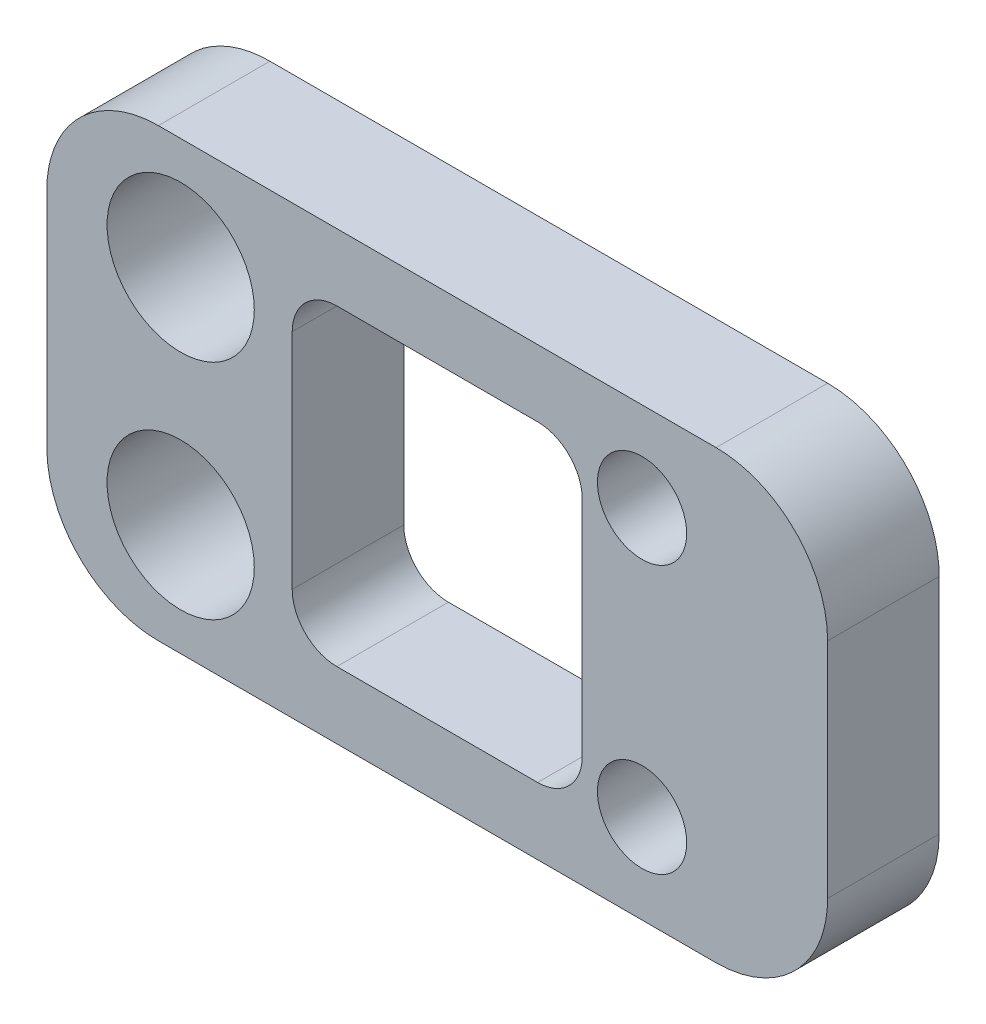
SolidWorks part; units mm, degrees
ref_plane "Plan de face" through (0, 0, 0) normal (0, 0, 1) x (1, 0, 0)
ref_plane "Plan de dessus" through (0, 0, 0) normal (0, 1, 0) x (1, 0, 0)
ref_plane "Plan de droite" through (0, 0, 0) normal (1, 0, 0) x (0, 0, -1)
sketch "Esquisse1" plane through (0, 0, 0) normal (0, 0, 1) x (1, 0, 0)
  line L1 (-48.7729, 33.8508) -> (-13.7729, 33.8508)
  line L2 (-48.7729, 33.8508) -> (-48.7729, 13.8508)
  line L3 (-48.7729, 13.8508) -> (-13.7729, 13.8508)
  line L4 (-13.7729, 33.8508) -> (-13.7729, 13.8508)
  line L5 (-48.7729, 33.8508) -> (-13.7729, 13.8508) construction
  line L6 (-48.7729, 13.8508) -> (-13.7729, 33.8508) construction
  point P0 (-31.2729, 23.8508)
  dimension "D1" = 20
  dimension "D2" = 35
extrude "Boss.-Extru.1" add sketch "Esquisse1" along normal blind 5
fillet "Congé1" radius 5 4 edges at (-13.7729, 13.8508, 2.5) (-13.7729, 33.8508, 2.5) (-48.7729, 13.8508, 2.5) (-48.7729, 33.8508, 2.5)
sketch "Esquisse6" plane through (0, 0, 5) normal (0, 0, 1) x (1, 0, 0)
  line L1 (-43.7729, 33.8508) -> (-18.7729, 33.8508) construction
  line L2 (-48.7729, 28.8508) -> (-48.7729, 18.8508) construction
  line L3 (-43.7729, 13.8508) -> (-18.7729, 13.8508) construction
  circle A0 centre (-42.7729, 28.8508) radius 3.3
  circle A1 centre (-42.7729, 18.8508) radius 3.3
  dimension "D1" = 5
  dimension "D4" = 5
  dimension "D2" = 6
  dimension "D3" = 20
sketch "Esquisse7" plane through (0, 0, 5) normal (0, 0, 1) x (1, 0, 0)
  line L0 (-43.7729, 13.8508) -> (-18.7729, 13.8508) construction
  circle A0 centre (-22.092, 29.8508) radius 2
  circle A1 centre (-22.092, 17.8508) radius 2
  dimension "D1" = 12
  dimension "D2" = 4
extrude "Enlèv. mat.-Extru.2" cut sketch "Esquisse7" against normal blind 10
extrude "Enlèv. mat.-Extru.3" cut sketch "Esquisse6" against normal blind 10
sketch "Esquisse9" plane through (0, 0, 5) normal (0, 0, 1) x (1, 0, 0)
  line L0 (-43.7729, 33.8508) -> (-18.7729, 33.8508) construction
  line L1 (-37.7729, 30.8508) -> (-24.7729, 30.8508)
  line L2 (-37.7729, 30.8508) -> (-37.7729, 16.8508)
  line L3 (-37.7729, 16.8508) -> (-24.7729, 16.8508)
  line L4 (-24.7729, 30.8508) -> (-24.7729, 16.8508)
  line L5 (-37.7729, 30.8508) -> (-24.7729, 16.8508) construction
  line L6 (-37.7729, 16.8508) -> (-24.7729, 30.8508) construction
  line L7 (-43.7729, 13.8508) -> (-18.7729, 13.8508) construction
  line L8 (-48.7729, 28.8508) -> (-48.7729, 18.8508) construction
  line L9 (-13.7729, 28.8508) -> (-13.7729, 18.8508) construction
  point P0 (-31.2729, 23.8508)
  dimension "D1" = 3
  dimension "D2" = 3
  dimension "D3" = 11
  dimension "D4" = 11
extrude "Enlèv. mat.-Extru.5" cut sketch "Esquisse9" against normal blind 10
fillet "Congé2" radius 2 4 edges at (-37.7729, 16.8508, 2.5) (-24.7729, 16.8508, 2.5) (-24.7729, 30.8508, 2.5) (-37.7729, 30.8508, 2.5)
